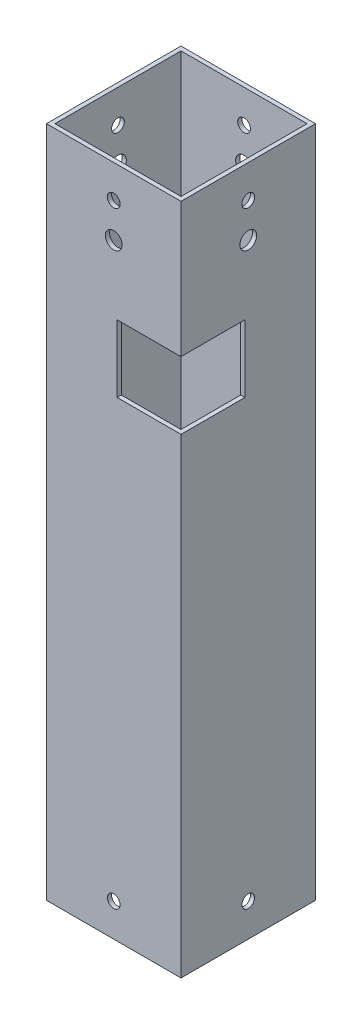
SolidWorks part; units mm, degrees
material "6061 Alloy"
ref_plane "Front Plane" through (0, 0, 0) normal (0, 0, 1) x (1, 0, 0)
ref_plane "Top Plane" through (0, 0, 0) normal (0, 1, 0) x (1, 0, 0)
ref_plane "Right Plane" through (0, 0, 0) normal (1, 0, 0) x (0, 0, -1)
sketch "Sketch1" plane through (0, 0, 0) normal (0, 1, 0) x (1, 0, 0)
  line L1 (-23.8125, 23.8125) -> (23.8125, 23.8125)
  line L2 (-23.8125, 23.8125) -> (-23.8125, -23.8125)
  line L3 (-23.8125, -23.8125) -> (23.8125, -23.8125)
  line L4 (23.8125, 23.8125) -> (23.8125, -23.8125)
  line L5 (-25.4, 25.4) -> (25.4, 25.4)
  line L6 (-25.4, 25.4) -> (-25.4, -25.4)
  line L7 (-25.4, -25.4) -> (25.4, -25.4)
  line L8 (25.4, 25.4) -> (25.4, -25.4)
  point P2 (-25.4, 0)
  point P11 (-23.8125, 0)
  point P12 (0, 23.8125)
  point P13 (0, 25.4)
  dimension "D1" = 47.625
  dimension "D2" = 50.8
  dimension "2.05" = 50.8
  dimension "D3" = 47.625
extrude "Boss-Extrude1" add sketch "Sketch1" along normal blind 254
ref_plane "Plane1" through (0, 152.4, 0) normal (0, 1, 0) x (1, 0, 0)
sketch "Sketch3" plane through (0, 152.4, 0) normal (0, 1, 0) x (1, 0, 0)
  line L1 (-23.8125, 23.8125) -> (23.8125, 23.8125)
  line L2 (-23.8125, 23.8125) -> (-23.8125, -23.8125)
  line L3 (-23.8125, -23.8125) -> (23.8125, -23.8125)
  line L4 (23.8125, 23.8125) -> (23.8125, -23.8125)
sketch "Sketch4" plane through (-23.8125, 0, 0) normal (1, 0, 0) x (0, 0, -1)
  line L0 (-25.4, 254) -> (25.4, 254) construction
  line L1 (25.4, 254) -> (25.4, 0) construction
  circle A0 centre (0, 241.5876) radius 2.4
  dimension "D1" = 4.8
  dimension "D2" = 12.4124
  dimension "D3" = 25.4
extrude "Cut-Extrude1" cut sketch "Sketch4" along normal through all both and the other way through all
sketch "Sketch5" plane through (0, 0, -25.4) normal (0, 0, -1) x (-1, 0, 0)
  line L0 (-25.4, 254) -> (25.4, 254) construction
  line L1 (25.4, 254) -> (25.4, 0) construction
  circle A0 centre (0, 241.5876) radius 2.4
  dimension "D1" = 4.8
  dimension "D2" = 12.4124
  dimension "D3" = 25.4
extrude "Cut-Extrude2" cut sketch "Sketch5" against normal through all
sketch "Sketch6" plane through (25.4, 0, 0) normal (1, 0, 0) x (0, 0, -1)
  line L0 (-25.4, 0) -> (25.4, 0) construction
  line L1 (25.4, 254) -> (25.4, 0) construction
  circle A0 centre (0, 12.4124) radius 2.4
  dimension "D1" = 12.4124
  dimension "D2" = 4.8
  dimension "D3" = 25.4
extrude "Cut-Extrude3" cut sketch "Sketch6" against normal through all both and the other way through all
sketch "Sketch7" plane through (0, 0, -25.4) normal (0, 0, -1) x (-1, 0, 0)
  line L0 (-25.4, 0) -> (25.4, 0) construction
  circle A0 centre (0, 12.4124) radius 2.4
  dimension "D1" = 4.8
  dimension "D2" = 12.4124
  dimension "D3" = 25.4
extrude "Cut-Extrude4" cut sketch "Sketch7" against normal through all both
sketch "Sketch8" plane through (0, 0, -25.4) normal (0, 0, -1) x (-1, 0, 0)
  line L0 (-25.4, 254) -> (25.4, 254) construction
  line L1 (-25.4, 254) -> (-25.4, 0) construction
  circle A0 centre (0, 228.6) radius 3.175
  dimension "D1" = 6.35
  dimension "D2" = 25.4
  dimension "D3" = 25.4
extrude "Cut-Extrude5" cut sketch "Sketch8" against normal through all both and the other way through all
sketch "Sketch9" plane through (25.4, 0, 0) normal (1, 0, 0) x (0, 0, -1)
  line L0 (-25.4, 254) -> (25.4, 254) construction
  line L1 (-25.4, 254) -> (-25.4, 0) construction
  circle A0 centre (0, 228.6) radius 3.175
  dimension "D1" = 6.35
  dimension "D2" = 25.4
  dimension "D3" = 25.4
extrude "Cut-Extrude6" cut sketch "Sketch9" against normal through all both
sketch "Sketch10" plane through (25.4, 0, 0) normal (1, 0, 0) x (0, 0, -1)
  line L0 (-25.4, 254) -> (-25.4, 0) construction
  line L1 (-25.4, 203.2) -> (-1.27, 203.2)
  line L2 (-25.4, 203.2) -> (-25.4, 177.8)
  line L3 (-25.4, 177.8) -> (-1.27, 177.8)
  line L4 (-1.27, 203.2) -> (-1.27, 177.8)
  line L5 (-25.4, 254) -> (25.4, 254) construction
  dimension "D1" = 50.8
  dimension "D2" = 25.4
  dimension "D3" = 24.13
extrude "Cut-Extrude7" cut sketch "Sketch10" against normal blind 24.13
